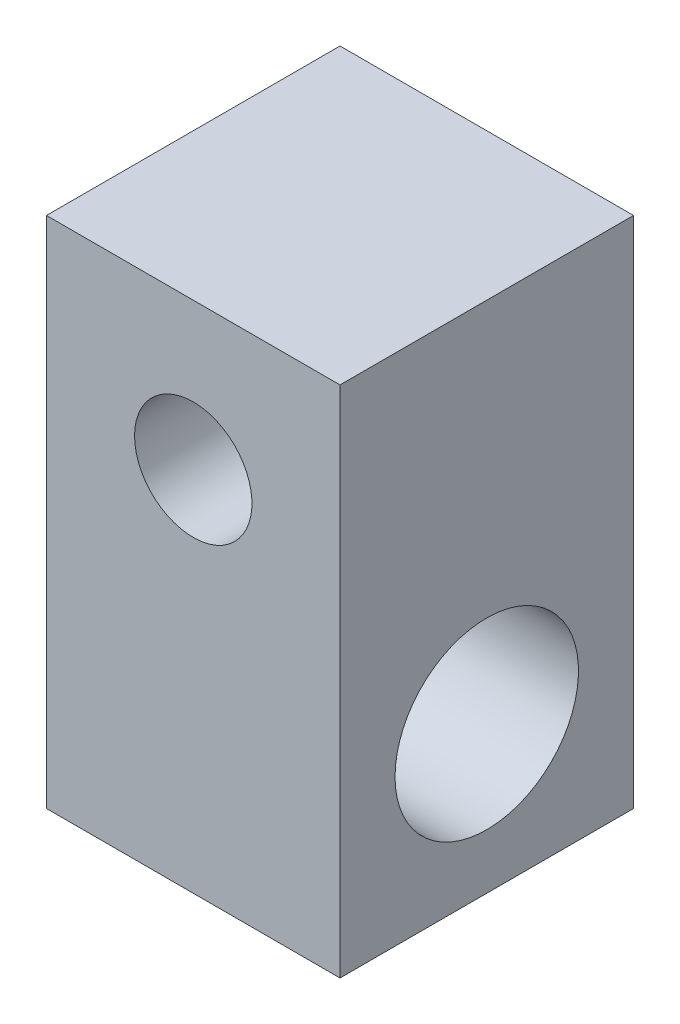
SolidWorks part; units mm, degrees
ref_plane "Front Plane" through (0, 0, 0) normal (0, 0, 1) x (1, 0, 0)
ref_plane "Top Plane" through (0, 0, 0) normal (0, 1, 0) x (1, 0, 0)
ref_plane "Right Plane" through (0, 0, 0) normal (1, 0, 0) x (0, 0, -1)
sketch "Sketch1" plane through (0, 0, 0) normal (0, 0, 1) x (1, 0, 0)
  line L1 (4, -7) -> (-4, -7)
  line L2 (4, -7) -> (4, 7)
  line L3 (4, 7) -> (-4, 7)
  line L4 (-4, -7) -> (-4, 7)
  line L5 (4, -7) -> (-4, 7) construction
  line L6 (4, 7) -> (-4, -7) construction
  point P0 (0, 0)
  dimension "D1" = 14
  dimension "D2" = 8
extrude "Boss-Extrude1" add sketch "Sketch1" along normal blind 8
sketch "Sketch2" plane through (0, 0, 0) normal (0, 0, -1) x (-1, 0, 0)
  line L0 (-4, 7) -> (4, 7) construction
  circle A0 centre (0, 3) radius 1.6
  point P2 (0, 7)
  dimension "D1" = 3.2
  dimension "D2" = 4
extrude "Cut-Extrude1" cut sketch "Sketch2" against normal through all
sketch "Sketch4" plane through (-4, 0, 0) normal (-1, 0, 0) x (0, 0, 1)
  line L0 (8, -7) -> (0, -7) construction
  line L1 (8, 7) -> (0, 7) construction
  circle A0 centre (4, -3) radius 2.5
  point P2 (4, -7)
  dimension "D1" = 5
  dimension "D2" = 4
  dimension "D3" = 10
extrude "Cut-Extrude2" cut sketch "Sketch4" against normal through all
